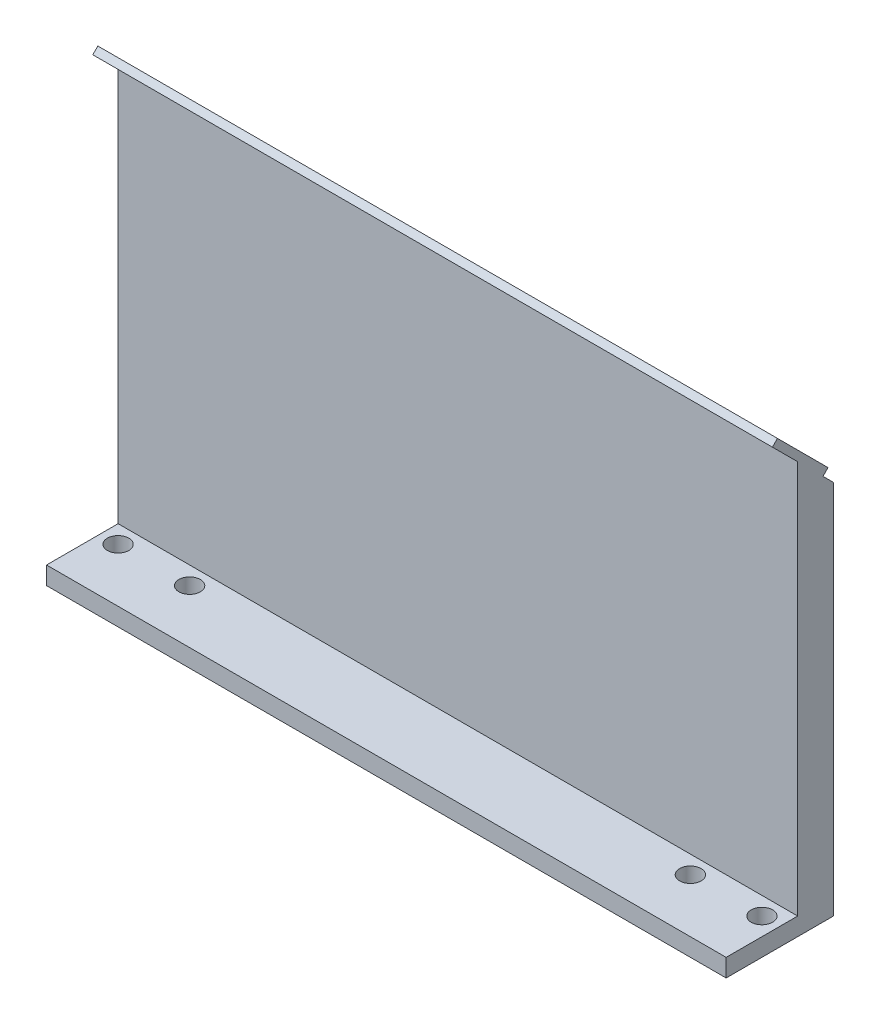
SolidWorks part; units mm, degrees
ref_plane "Front Plane" through (0, 0, 0) normal (0, 0, 1) x (1, 0, 0)
ref_plane "Top Plane" through (0, 0, 0) normal (0, 1, 0) x (1, 0, 0)
ref_plane "Right Plane" through (0, 0, 0) normal (1, 0, 0) x (0, 0, -1)
sketch "Sketch1" plane through (0, 0, 0) normal (0, 1, 0) x (1, 0, 0)
  line L1 (-95.8439, 31.9784) -> (145.4561, 31.9784)
  line L2 (-95.8439, 31.9784) -> (-95.8439, -6.1216)
  line L3 (-95.8439, -6.1216) -> (145.4561, -6.1216)
  line L4 (145.4561, 31.9784) -> (145.4561, -6.1216)
  dimension "D1" = 241.3
  dimension "D2" = 38.1
extrude "Boss-Extrude1" add sketch "Sketch1" along normal blind 6.35
sketch "Sketch2" plane through (0, 6.35, 0) normal (0, 1, 0) x (1, 0, 0)
  line L0 (-95.8439, 31.9784) -> (-95.8439, -6.1216) construction
  line L1 (145.4561, 31.9784) -> (-95.8439, 31.9784) construction
  circle A0 centre (-89.4939, 12.9284) radius 3.81
  circle A1 centre (-64.0939, 12.9284) radius 3.81
  circle A2 centre (-38.6939, 12.9284) radius 3.81
  circle A3 centre (-13.2939, 12.9284) radius 3.81
  circle A4 centre (12.1061, 12.9284) radius 3.81
  circle A5 centre (37.5061, 12.9284) radius 3.81
  circle A6 centre (62.9061, 12.9284) radius 3.81
  circle A7 centre (88.3061, 12.9284) radius 3.81
  circle A8 centre (113.7061, 12.9284) radius 3.81
  circle A9 centre (139.1061, 12.9284) radius 3.81
  dimension "D1" = 7.62
  dimension "D3" = 6.35
  dimension "D4" = 19.05
  dimension "D2" = 10
extrude "Cut-Extrude1" cut sketch "Sketch2" against normal through all contours A0 | A1 | A9 | A8
sketch "Sketch3" plane through (0, 6.35, 0) normal (0, 1, 0) x (1, 0, 0)
  line L0 (145.4561, 31.9784) -> (-95.8439, 31.9784) construction
  line L1 (-95.8439, 31.9784) -> (145.4561, 31.9784)
  line L2 (-95.8439, 31.9784) -> (-95.8439, 19.2784)
  line L3 (-95.8439, 19.2784) -> (145.4561, 19.2784)
  line L4 (145.4561, 31.9784) -> (145.4561, 19.2784)
  line L5 (-95.8439, 31.9784) -> (-95.8439, -6.1216) construction
  line L6 (145.4561, -6.1216) -> (145.4561, 31.9784) construction
  dimension "D1" = 12.7
extrude "Boss-Extrude2" add sketch "Sketch3" along normal blind 139.7
sketch "Sketch8" plane through (-95.8439, 0, 0) normal (-1, 0, 0) x (0, 0, 1)
  line L2 (-31.9784, 146.05) -> (-31.9784, 133.35)
  line L5 (-31.9784, 133.35) -> (-19.2784, 146.05)
  line L7 (-34.5184, 133.35) -> (-31.9784, 133.35)
  line L9 (-34.5184, 133.35) -> (-34.5184, 148.59)
  line L10 (-34.5184, 148.59) -> (-19.2784, 148.59)
  line L11 (-19.2784, 148.59) -> (-19.2784, 146.05)
  line L12 (-19.2784, 146.05) -> (-31.9784, 146.05) construction
  line M9 (-19.2784, 146.05) -> (-31.9784, 146.05)
  line M10 (-31.9784, 146.05) -> (-31.9784, 0)
  dimension "D1" = 45
  dimension "D2" = 12.7
  dimension "D3" = 2.54
  dimension "D4" = 2.54
extrude "Cut-Extrude4" cut sketch "Sketch8" against normal through all contours L5 M10 M9 | L11 L10 L9 L7 M10 M9
sketch "Sketch9" plane through (-95.8439, 0, 0) normal (-1, 0, 0) x (0, 0, 1)
  line L1 (-30.0547, 138.8658) -> (-12.0942, 156.8263)
  line L2 (-30.0547, 138.8658) -> (-28.2587, 137.0697)
  line L3 (-28.2587, 137.0697) -> (-10.2982, 155.0303)
  line L4 (-12.0942, 156.8263) -> (-10.2982, 155.0303)
  line L9 (-31.9784, 133.35) -> (-19.2784, 146.05) construction
  point P4 (-31.0264, 144.9574)
  point P7 (-19.2784, 146.05)
  point P9 (0, 0)
  point P10 (0, 0)
  dimension "D1" = 25.4
  dimension "D2" = 2.54
extrude "Boss-Extrude5" add sketch "Sketch9" against normal up to surface (241.3 mm away) up to face at (145.4561, 48.6833, -15.0451)
